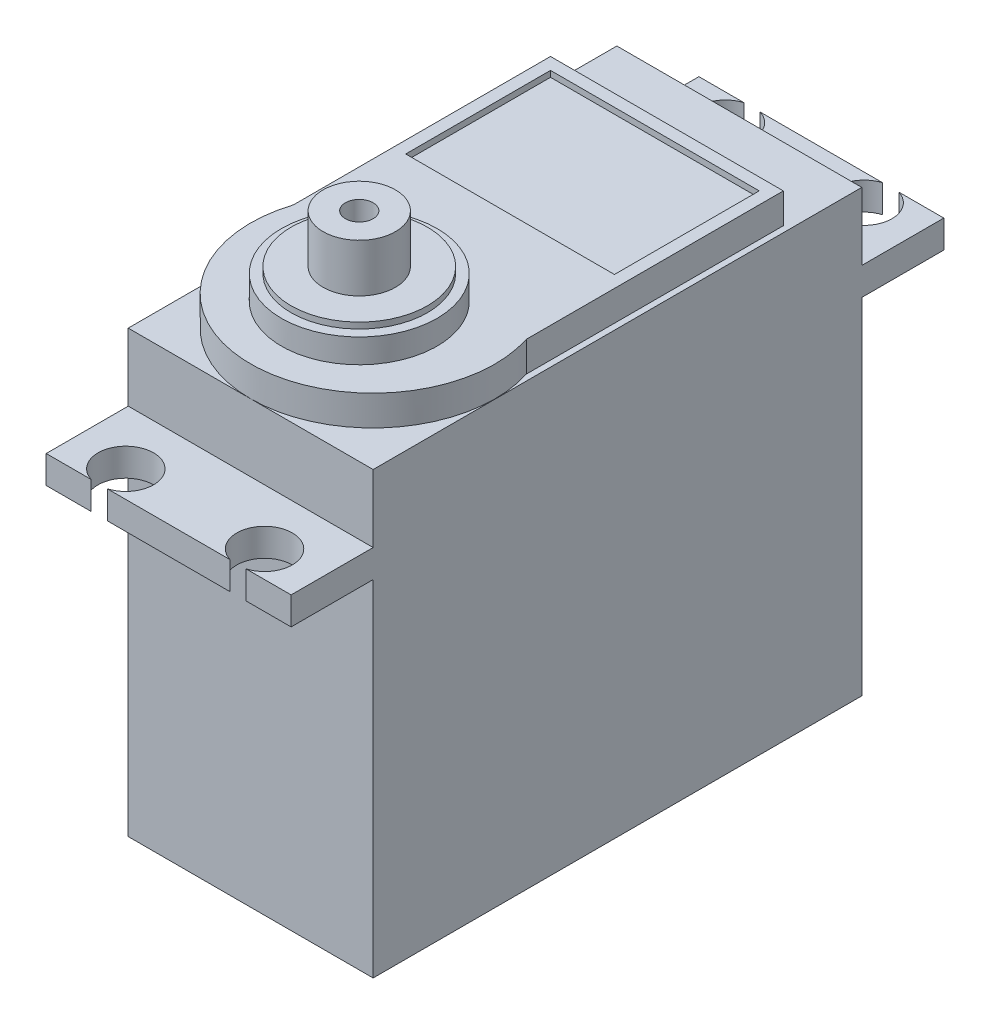
SolidWorks part; units mm, degrees
ref_plane "Front Plane" through (0, 0, 0) normal (0, 0, 1) x (1, 0, 0)
ref_plane "Top Plane" through (0, 0, 0) normal (0, 1, 0) x (1, 0, 0)
ref_plane "Right Plane" through (0, 0, 0) normal (1, 0, 0) x (0, 0, -1)
sketch "Sketch1" plane through (0, 0, 0) normal (0, 1, 0) x (1, 0, 0)
  line L1 (-10.15, -20.25) -> (10.15, -20.25)
  line L2 (-10.15, -20.25) -> (-10.15, 20.25)
  line L3 (-10.15, 20.25) -> (10.15, 20.25)
  line L4 (10.15, -20.25) -> (10.15, 20.25)
  line L5 (-10.15, -20.25) -> (10.15, 20.25) construction
  line L6 (-10.15, 20.25) -> (10.15, -20.25) construction
  point P0 (0, 0)
  dimension "D1" = 40.5
  dimension "D2" = 20.3
extrude "Boss-Extrude1" add sketch "Sketch1" along normal blind 36.5
sketch "Sketch4" plane through (0, 0, 20.25) normal (0, 0, 1) x (1, 0, 0)
  line L0 (10.15, 0) -> (10.15, 28.6) construction
  line L1 (10.15, 36.5) -> (10.15, 0) construction
  line L2 (10.15, 28.6) -> (-10.15, 28.6)
  line L3 (-10.15, 36.5) -> (-10.15, 0) construction
  line L4 (-10.15, 28.6) -> (-10.15, 30.9)
  line L5 (-10.15, 30.9) -> (10.15, 30.9)
  line L6 (10.15, 30.9) -> (10.15, 28.6)
  dimension "D1" = 28.6
  dimension "D2" = 2.3
extrude "Boss-Extrude4" add sketch "Sketch4" along normal blind 6.8 contours L5 L6 L2 L4
sketch "Sketch5" plane through (0, 30.9, 0) normal (0, 1, 0) x (1, 0, 0)
  line L0 (0, -20.25) -> (0, -22.35) construction
  line L1 (-10.15, -20.25) -> (10.15, -20.25) construction
  line L2 (-10.15, -22.35) -> (10.15, -22.35) construction
  line L3 (10.15, -27.05) -> (10.15, -20.25) construction
  line L4 (0, -22.35) -> (0, -27.05) construction
  line L5 (-10.15, -27.05) -> (10.15, -27.05) construction
  line L7 (10.15, -27.05) -> (8.05, -27.05) construction
  line L8 (8.05, -27.05) -> (5.75, -27.05)
  line L9 (5.75, -27.05) -> (5.75, -24.85)
  circle A0 centre (5.75, -24.85) radius 2.3
  circle A1 centre (-5.75, -24.85) radius 2.3
  point P10 (0, -22.35)
  dimension "D2" = 4.6
  dimension "D1" = 2.1
  dimension "D3" = 2.1
  dimension "D4" = 2.2
  dimension "D5" = 2.3
extrude "Cut-Extrude1" cut sketch "Sketch5" against normal up to body (2.3 mm away)
sketch "Sketch6" plane through (-10.15, 0, 0) normal (-1, 0, 0) x (0, 0, 1)
  line L0 (0, 0) -> (0, 36.5) construction
  line L1 (-20.25, 0) -> (20.25, 0) construction
  line L2 (-20.25, 36.5) -> (20.25, 36.5) construction
ref_plane "Plane1" through (0, 0, 0) normal (0, 0, 1) x (0, 1, 0)
mirror "Mirror2" about plane through (0, 0, 0) normal (0, 0, 1) of "Cut-Extrude1", "Boss-Extrude4"
sketch "Sketch7" plane through (0, 36.5, 0) normal (0, 1, 0) x (1, 0, 0)
  line L0 (10.15, 20.25) -> (-10.15, 20.25) construction
  line L1 (10.15, -20.25) -> (10.15, 20.25) construction
  line L2 (10.15, 14.75) -> (-10.15, 14.75)
  line L3 (-10.15, 20.25) -> (-10.15, -20.25) construction
  line L4 (-10.15, 14.75) -> (-10.15, -7.05)
  line L5 (10.15, 14.75) -> (10.15, -7.05) construction
  line L6 (0, -20.25) -> (0, 11.25) construction
  line L7 (-10.15, -20.25) -> (10.15, -20.25) construction
  line L8 (-9.65, 14.25) -> (-9.65, -7.05)
  line L9 (9.65, 14.25) -> (-9.65, 14.25)
  line L10 (9.65, 14.25) -> (9.65, -7.05)
  arc A0 (9.65, -7.05) -> (-9.65, -7.05) centre (0, -10.1226) cw
  dimension "D1" = 5.5
  dimension "D2" = 13.2
  dimension "D3" = 31.5
  dimension "D4" = 0.5
extrude "Boss-Extrude5" add sketch "Sketch7" along normal blind 2.5 contours A0 L8 L9 L10
sketch "Sketch10" plane through (0, 39, 0) normal (0, 1, 0) x (1, 0, 0)
  line L0 (0, -20.25) -> (0, -11.25) construction
  arc A0 (-9.65, -7.05) -> (9.65, -7.05) centre (0, -10.1226) ccw construction
  circle A1 centre (0, -11.25) radius 6.45
  dimension "D2" = 12.9
  dimension "D1" = 9
extrude "Boss-Extrude6" add sketch "Sketch10" along normal blind 2
sketch "Sketch11" plane through (0, 41, 0) normal (0, 1, 0) x (1, 0, 0)
  circle A0 centre (0, -11.25) radius 6.45 construction
  circle A1 centre (0, -11.25) radius 5.65
  dimension "D1" = 0.8
extrude "Boss-Extrude7" add sketch "Sketch11" along normal blind 0.5
sketch "Sketch12" plane through (0, 41.5, 0) normal (0, 1, 0) x (1, 0, 0)
  circle A0 centre (0, -11.25) radius 3
  dimension "D1" = 6
extrude "Boss-Extrude8" add sketch "Sketch12" along normal blind 4
sketch "Sketch13" plane through (0, 45.5, 0) normal (0, 1, 0) x (1, 0, 0)
  circle A0 centre (0, -11.25) radius 1.15
  dimension "D1" = 2.3
extrude "Cut-Extrude2" cut sketch "Sketch13" against normal blind 4
sketch "Sketch14" plane through (0, 39, 0) normal (0, 1, 0) x (1, 0, 0)
  line L0 (9.65, 14.25) -> (-9.65, 14.25) construction
  line L1 (-8.65, 13.25) -> (8.65, 13.25)
  line L2 (-8.65, 13.25) -> (-8.65, 1.25)
  line L3 (-8.65, 1.25) -> (8.65, 1.25)
  line L4 (8.65, 13.25) -> (8.65, 1.25)
  line L5 (-9.65, 14.25) -> (-9.65, -7.05) construction
  line L6 (9.65, 14.25) -> (9.65, -7.05) construction
  dimension "D1" = 1
  dimension "D2" = 1
  dimension "D3" = 1
  dimension "D4" = 12
extrude "Cut-Extrude3" cut sketch "Sketch14" against normal blind 0.5
equation "\"SpoolCenterToMotor\"= 31.5mm"
equation "\"D3@Sketch7\"=\"SpoolCenterToMotor\""
equation "\"MotorLength\"= 40.5mm"
equation "\"D1@Sketch1\"=\"MotorLength\""
equation "\"MotorWidth\"= 20.3mm"
equation "\"D2@Sketch1\"=\"MotorWidth\""
equation "\"AttachmentHeight\"= 3mm"
equation "\"SpoolDiameter\"= 60mm"
equation "\"SpoolHeight\"= 2mm"
equation "\"SpoolRidgeHeight\"= 1mm"
equation "\"SpoolRidgeDepth\"= 2mm"
equation "\"OuterThickness\"= 3mm"
equation "\"MasterFillet\"= 3mm"
equation "\"PartSeperation\"= 6mm"
equation "\"Tolerance\"= 0.15mm"
equation "\"HeightPart\"= 100mm"
equation "\"Holes\"= 1.5mm"
equation "\"SpineHolderThickness\"= 3mm"
equation "\"SpineHolderDepth\"= 3mm"
equation "\"MotorTransmitterToScrew\"= 21.7mm"
equation "\"SpoolSeperation\"= 2mm"
equation "\"ServoHolderWidthOffset\"= 20mm"
equation "\"DiscThickness\"= 4mm"
equation "\"LigamentThickness\"= 2mm"
equation "\"LigamentExtension\"= 1mm"
equation "\"LigamentAngle\"= 20deg"
equation "\"SpineDiameter\"= 15mm"
equation "\"LigamentDepth\"= 1mm"
equation "\"SpoolToSpine\"= 15mm"
equation "\"HubOffset\"= 18mm"
equation "\"ServoFastenerHolders\"=2mm"
equation "\"ArduinoLength\"= 53.4mm"
equation "\"ArduinoWidth\"= 50mm"
equation "\"ArdYOffset\"= 29.5mm"
equation "\"ArdXOffset\"= 20.5mm"
equation "\"ArdXOffsetSmall\"= 25mm"
equation "\"MiddleServoOffset\"= 12mm"
equation "\"LargeServoOffset\"= 3mm"
equation "\"SmallServoOffset\"= 0mm"
equation "\"ToolHoleDiameter\"= 12mm"
